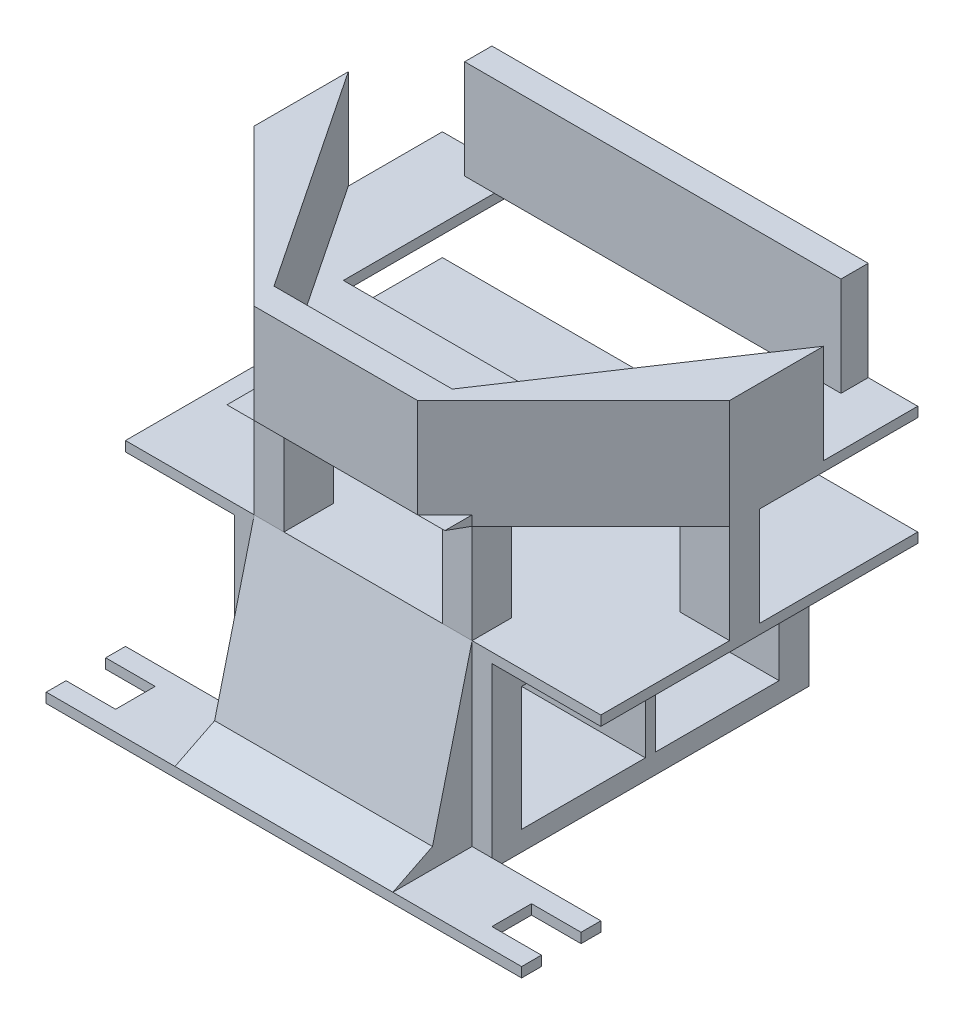
SolidWorks part; units mm, degrees
ref_plane "Ön Düzlem" through (0, 0, 0) normal (0, 0, 1) x (1, 0, 0)
ref_plane "Üst Düzlem" through (0, 0, 0) normal (0, 1, 0) x (1, 0, 0)
ref_plane "Sağ Düzlem" through (0, 0, 0) normal (1, 0, 0) x (0, 0, -1)
sketch "Sketch1" plane through (0, 0, 0) normal (1, 0, 0) x (0, 0, -1)
  line L1 (0, 0) -> (27, 0)
  line L2 (0, 0) -> (0, 18)
  line L3 (0, 18) -> (27, 18)
  line L4 (27, 0) -> (27, 18)
  dimension "D1" = 27
  dimension "D2" = 18
extrude "Boss-Extrude1" add sketch "Sketch1" along normal blind 26
sketch "Sketch2" plane through (26, 0, 0) normal (1, 0, 0) x (0, 0, -1)
  line L0 (0, 18) -> (0, 0) construction
  line L1 (3, 2) -> (15.5, 2)
  line L2 (3, 2) -> (3, 14.5)
  line L3 (3, 14.5) -> (15.5, 14.5)
  line L4 (15.5, 2) -> (15.5, 14.5)
  line L5 (0, 0) -> (27, 0) construction
  dimension "D1" = 12.5
  dimension "D2" = 12.5
  dimension "D3" = 3
  dimension "D4" = 2
extrude "Cut-Extrude1" cut sketch "Sketch2" against normal blind 26
sketch "Sketch4" plane through (0, 0, -27) normal (0, 0, -1) x (-1, 0, 0)
  line L1 (-26, 0) -> (0, 0)
  line L2 (-26, 0) -> (-26, 18)
  line L3 (-26, 18) -> (0, 18)
  line L4 (0, 0) -> (0, 18)
extrude "Boss-Extrude2" add sketch "Sketch4" along normal blind 5
sketch "Sketch5" plane through (26, 0, 0) normal (1, 0, 0) x (0, 0, -1)
  line L0 (15.5, 2) -> (15.5, 14.5) construction
  line L1 (16.5, 14.5) -> (29, 14.5)
  line L2 (16.5, 14.5) -> (16.5, 2)
  line L3 (16.5, 2) -> (29, 2)
  line L4 (29, 14.5) -> (29, 2)
  line L5 (0, 0) -> (32, 0) construction
  dimension "D1" = 12.5
  dimension "D2" = 12.5
  dimension "D3" = 1
  dimension "D4" = 2
extrude "Cut-Extrude2" cut sketch "Sketch5" against normal blind 26
sketch "Sketch7" plane through (0, 0, 0) normal (0, 0, 1) x (1, 0, 0)
  line L0 (26, 18) -> (26, 0) construction
  line L1 (0, 0) -> (26, 0)
  line L2 (0, 0) -> (0, 1)
  line L3 (0, 1) -> (26, 1)
  line L4 (26, 0) -> (26, 1)
  dimension "D1" = 1
extrude "Boss-Extrude3" add sketch "Sketch7" along normal blind 8
sketch "Sketch8" plane through (0, 1, 0) normal (0, 1, 0) x (1, 0, 0)
  line L2 (-11, -8) -> (37, -8)
  line L3 (-11, -8) -> (-11, 0)
  line L4 (-11, 0) -> (37, 0)
  line L6 (37, -8) -> (37, 0)
  dimension "D1" = 11
  dimension "D2" = 11
extrude "Boss-Extrude4" add sketch "Sketch8" against normal up to surface (1 mm away) up to face at (13, 0, -12)
sketch "Sketch9" plane through (0, 1, 0) normal (0, 1, 0) x (1, 0, 0)
  line L0 (-11, 0) -> (-11, -8) construction
  line L1 (-11, -2) -> (-6, -2)
  line L2 (-11, -2) -> (-11, -6)
  line L3 (-11, -6) -> (-6, -6)
  line L4 (-6, -2) -> (-6, -6)
  line L5 (37, -8) -> (37, 0) construction
  line L6 (37, -6) -> (32, -6)
  line L7 (37, -6) -> (37, -2)
  line L8 (37, -2) -> (32, -2)
  line L9 (32, -6) -> (32, -2)
  dimension "D1" = 2
  dimension "D2" = 2
  dimension "D3" = 5
  dimension "D4" = 5
extrude "Cut-Extrude4" cut sketch "Sketch9" against normal blind 8
sketch "Sketch10" plane through (0, 18, 0) normal (0, 1, 0) x (1, 0, 0)
  line L1 (-11, 0) -> (37, 0)
  line L2 (-11, 0) -> (-11, 32)
  line L3 (-11, 32) -> (37, 32)
  line L4 (37, 0) -> (37, 32)
  dimension "D1" = 0
  dimension "D2" = 0
extrude "Boss-Extrude5" add sketch "Sketch10" along normal blind 1
sketch "Sketch12" plane through (0, 19, 0) normal (0, 1, 0) x (1, 0, 0)
  line L0 (-11, 32) -> (-11, 0) construction
  line L1 (-11, 16) -> (-6, 16)
  line L2 (-11, 16) -> (-11, 13)
  line L3 (-11, 13) -> (-6, 13)
  line L4 (-6, 16) -> (-6, 13)
  line L5 (37, 0) -> (37, 32) construction
  line L6 (37, 13) -> (32, 13)
  line L7 (37, 13) -> (37, 16)
  line L8 (37, 16) -> (32, 16)
  line L9 (32, 13) -> (32, 16)
  dimension "D1" = 16
  dimension "D2" = 16
  dimension "D3" = 3
  dimension "D4" = 3
  dimension "D5" = 5
  dimension "D6" = 5
extrude "Boss-Extrude7" add sketch "Sketch12" along normal blind 10
sketch "Sketch14" plane through (0, 19, 0) normal (0, 1, 0) x (1, 0, 0)
  line L0 (-11, 0) -> (37, 0) construction
  line L1 (2, 0) -> (5, 0)
  line L2 (2, 0) -> (2, 5)
  line L3 (2, 5) -> (5, 5)
  line L4 (5, 0) -> (5, 5)
  line L5 (26, 0) -> (0, 0) construction
  line L6 (21, 0) -> (24, 0)
  line L7 (21, 0) -> (21, 4)
  line L8 (21, 4) -> (24, 4)
  line L9 (24, 0) -> (24, 4)
  dimension "D1" = 5
  dimension "D2" = 3
  dimension "D3" = 3
  dimension "D4" = 4
  dimension "D5" = 16
  dimension "D6" = 13
extrude "Boss-Extrude8" add sketch "Sketch14" along normal blind 10
sketch "Sketch15" plane through (0, 29, 0) normal (0, 1, 0) x (1, 0, 0)
  line L0 (2, 0) -> (-11, 13)
  line L1 (-11, 13) -> (-11, 16)
  line L2 (-11, 16) -> (-11, 32)
  line L3 (-11, 32) -> (37, 32)
  line L4 (37, 32) -> (37, 13)
  line L5 (37, 13) -> (24, 0)
  line L6 (24, 0) -> (2, 0)
extrude "Boss-Extrude9" add sketch "Sketch15" along normal blind 1
sketch "Sketch17" plane through (0, 30, 0) normal (0, 1, 0) x (1, 0, 0)
  line L0 (37, 32) -> (-11, 32) construction
  line L1 (-6, 32) -> (32, 32)
  line L2 (-6, 32) -> (-6, 29.2486)
  line L3 (-6, 29.2486) -> (32, 29.2486)
  line L4 (32, 32) -> (32, 29.2486)
  line L5 (-11, 32) -> (-11, 13) construction
  dimension "D1" = 38
  dimension "D2" = 5
extrude "Boss-Extrude11" add sketch "Sketch17" along normal blind 10
sketch "Sketch18" plane through (0, 30, 0) normal (0, 1, 0) x (1, 0, 0)
  line L0 (2, 0) -> (4.7514, -2.7514)
  line L1 (-11, 13) -> (2, 0) construction
  line L2 (4.7514, -2.7514) -> (21.2486, -2.7514)
  line L3 (24, 0) -> (37, 13) construction
  line L4 (21.2486, -2.7514) -> (24, 0)
  line L5 (24, 0) -> (2, 0)
  dimension "D1" = 32
extrude "Boss-Extrude12" add sketch "Sketch18" along normal blind 10 separate body
ref_plane "Plane1" through (2, 30, 0) normal (-1, 0, 0) x (0, 0, 1)
sketch "Sketch19" plane through (2, 30, 0) normal (-1, 0, 0) x (0, 0, 1)
  line L0 (0, -1) -> (2.7514, 0)
  line L1 (2.7514, 0) -> (0, 0)
  line L2 (0, 0) -> (0, -1)
extrude "Boss-Extrude13" add sketch "Sketch19" against normal up to vertex (22 mm away)
sketch "Sketch21" plane through (0, 30, 0) normal (0, 1, 0) x (1, 0, 0)
  line L0 (32, 32) -> (-6, 32) construction
  line L1 (-3, 32) -> (29, 32)
  line L2 (-3, 32) -> (-3, 14)
  line L3 (-3, 14) -> (29, 14)
  line L4 (29, 32) -> (29, 14)
  dimension "D1" = 8
  dimension "D2" = 8
  dimension "D3" = 1
extrude "Cut-Extrude5" cut sketch "Sketch21" against normal blind 1
sketch "Sketch22" plane through (0, 0, 0) normal (0, 0, 1) x (1, 0, 0)
  line L0 (26, 1) -> (0, 1) construction
  line L1 (2, 1) -> (24, 1)
  line L2 (2, 1) -> (2, 19)
  line L3 (2, 19) -> (24, 19)
  line L4 (24, 1) -> (24, 19)
  line L5 (5, 19) -> (21, 19) construction
  line L6 (0, 18) -> (0, 1) construction
  dimension "D1" = 2
  dimension "D2" = 2
extrude "Boss-Extrude14" add sketch "Sketch22" along normal up to surface (8 mm away) up to face at (13, 0.5, 8)
sketch "Sketch23" plane through (24, 0, 0) normal (1, 0, 0) x (0, 0, -1)
  line L0 (0, 19) -> (-4, 3)
  line L1 (-4, 3) -> (-8, 1)
  line L2 (-8, 1) -> (-8, 19)
  line L3 (-8, 19) -> (0, 19)
  dimension "D1" = 2
  dimension "D2" = 4
extrude "Cut-Extrude6" cut sketch "Sketch23" against normal blind 40
sketch "Sketch25" plane through (0, 30, 0) normal (0, 1, 0) x (1, 0, 0)
  line L0 (24, 0) -> (37, 13)
  line L1 (37, 13) -> (37, 22.5)
  line L2 (37, 13) -> (37, 32) construction
  line L3 (37, 22.5) -> (22, 0)
  line L4 (2, 0) -> (-11, 13)
  line L5 (-11, 13) -> (-11, 22.5)
  line L6 (-11, 32) -> (-11, 13) construction
  line L7 (24, 0) -> (2, 0) construction
  line L8 (22, 0) -> (24, 0)
  line L9 (2, 0) -> (4, 0)
  line L10 (4, 0) -> (-11, 22.5)
  dimension "D1" = 2
  dimension "D2" = 2
extrude "Boss-Extrude17" add sketch "Sketch25" along normal up to surface (10 mm away) up to face at (13, 40, 1.3757)
